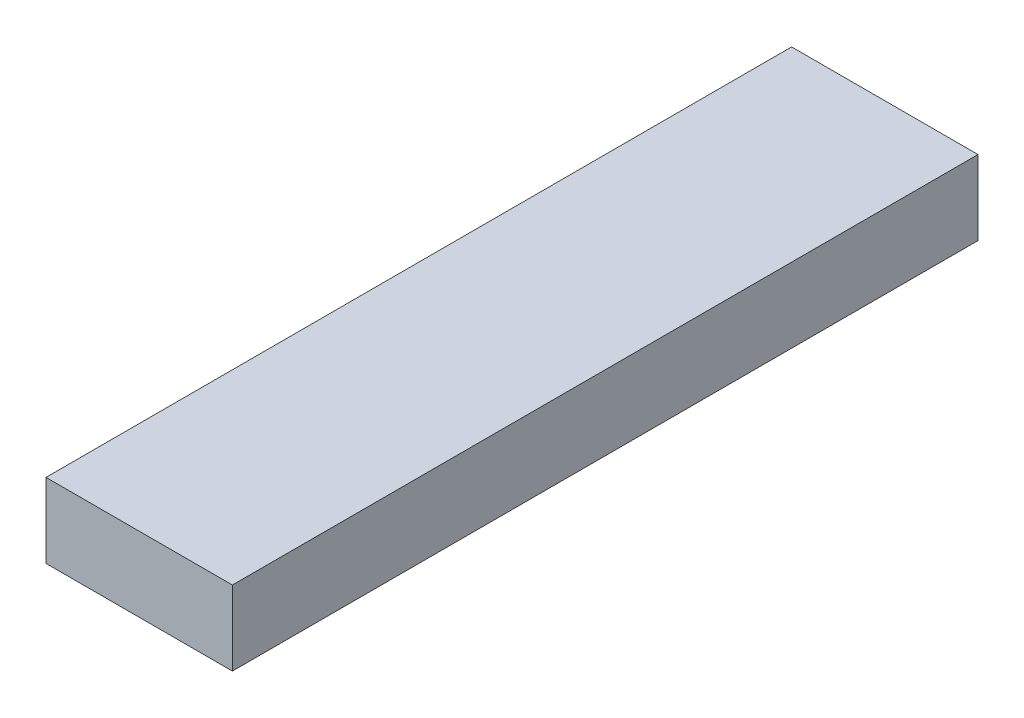
SolidWorks part; units mm, degrees
ref_plane "前视基准面" through (0, 0, 0) normal (0, 0, 1) x (1, 0, 0)
ref_plane "上视基准面" through (0, 0, 0) normal (0, 1, 0) x (1, 0, 0)
ref_plane "右视基准面" through (0, 0, 0) normal (1, 0, 0) x (0, 0, -1)
other "Configuration Table"
sketch "草图1" plane through (0, 0, 0) normal (0, 1, 0) x (1, 0, 0)
  line L0 (0, 0) -> (0, -200)
  line L1 (0, -200) -> (50, -200)
  line L2 (50, -200) -> (50, 0)
  line L3 (50, 0) -> (0, 0)
  dimension "D1" = 200
  dimension "D2" = 50
extrude "凸台-拉伸1" add sketch "草图1" along normal blind 20
